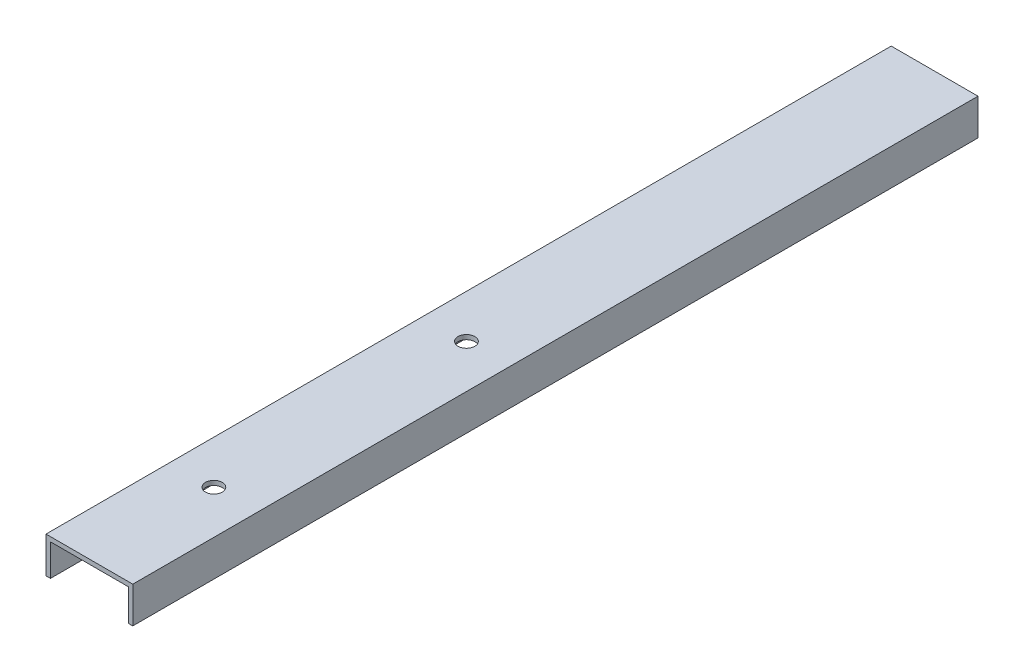
SolidWorks part; units mm, degrees
material "1023 Carbon Steel Sheet (SS)"
ref_plane "Front Plane" through (0, 0, 0) normal (0, 0, 1) x (1, 0, 0)
ref_plane "Top Plane" through (0, 0, 0) normal (0, 1, 0) x (1, 0, 0)
ref_plane "Right Plane" through (0, 0, 0) normal (1, 0, 0) x (0, 0, -1)
sketch "Sketch1" plane through (0, 0, 0) normal (0, 0, 1) x (1, 0, 0)
  line L0 (0, 0) -> (0, 10.2616)
  line L1 (0, 10.2616) -> (24.6126, 10.2616)
  line L2 (24.6126, 10.2616) -> (24.6126, 0)
  line L3 (24.6126, 0) -> (23.3426, 0)
  line L4 (23.3426, 0) -> (23.3426, 8.9916)
  line L5 (23.3426, 8.9916) -> (1.27, 8.9916)
  line L6 (1.27, 8.9916) -> (1.27, 0)
  line L7 (1.27, 0) -> (0, 0)
  dimension "D1" = 24.6126
  dimension "D2" = 10.2616
  dimension "D3" = 1.27
  dimension "D4" = 1.27
  dimension "D5" = 1.27
extrude "Boss-Extrude1" add sketch "Sketch1" along normal blind 239.7125
sketch "Sketch3" plane through (0, 10.2616, 0) normal (0, 1, 0) x (1, 0, 0)
  line L0 (12.3063, -239.7125) -> (12.3063, -204.4065) construction
  line L4 (24.6126, -239.7125) -> (0, -239.7125) construction
  line L5 (12.3063, -204.4065) -> (12.3063, -132.7785) construction
  circle A0 centre (12.3063, -204.4065) radius 2.3876
  circle A1 centre (12.3063, -132.7785) radius 2.3876
  dimension "D2" = 71.628
  dimension "D3" = 4.7752
  dimension "D1" = 35.306
extrude "Recognizer mount holes" cut sketch "Sketch3" against normal through all
ref_plane "Center plane" through (12.3063, 0, 0) normal (1, 0, 0) x (0, 0, -1)
equation "\"base length\"= 21"
equation "\"glass pane length\"= 14.125"
equation "\"glass pane width\"= 10.1875"
equation "\"glass pane wall width\"= 3/4"
equation "\"glass lip\"= 1/4"
equation "\"bolt diameter\"= 0.2"
equation "\"stepper body width\"= 2.22"
equation "\"stepper mount offset\"= 0.19"
equation "\"stepper mount diameter\"= 0.19"
equation "\"stepper shaft offset from body\"= 0.79"
equation "\"stepper spacer thickness\"= 0.2"
equation "\"y axis stepper wall height off base\"= 8"
equation "\"y axis stepper wall bracket thickness\"= 1"
equation "\"y axis stepper wall mount side offset\"= 1/2"
equation "\"y axis stepper wall mount top offset\"= 1/2"
equation "\"y axis stepper wall width\"= \"stepper body width\" + 1                  "
equation "\"thin metal\"= 0.12"
equation "\"thick metal\"= 0.25"
equation "\"recognizer width\"= 2.5"
equation "\"recognizer nut plate height\"= 1.25"
equation "\"recognizer nut plate offset\"= 1.5"
equation "\"recognizer arm length\"= 7"
equation "\"recognizer bracket length\"= 4"
